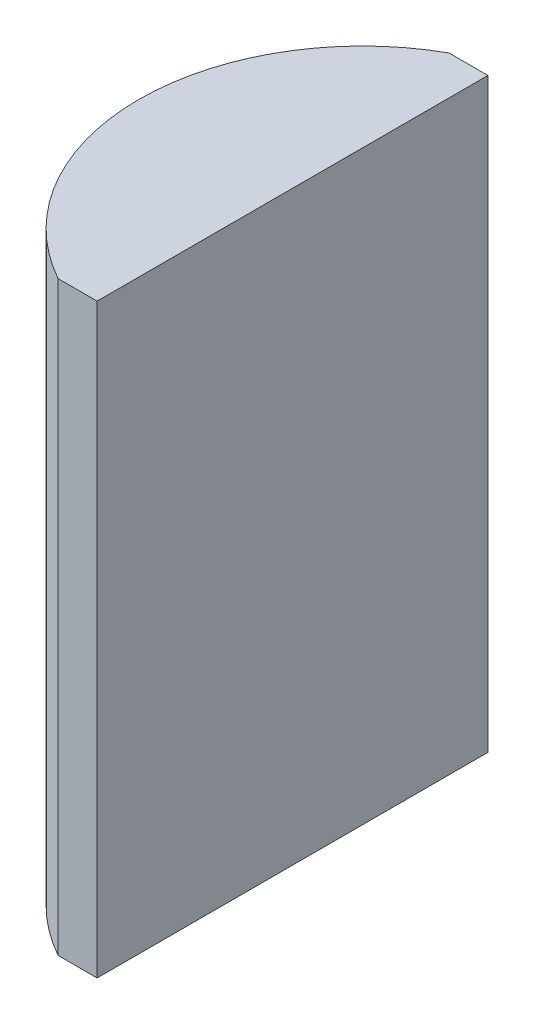
SolidWorks part; units mm, degrees
ref_plane "前视基准面" through (0, 0, 0) normal (0, 0, 1) x (1, 0, 0)
ref_plane "上视基准面" through (0, 0, 0) normal (0, 1, 0) x (1, 0, 0)
ref_plane "右视基准面" through (0, 0, 0) normal (1, 0, 0) x (0, 0, -1)
sketch "草图1" plane through (0, 0, 0) normal (0, 1, 0) x (1, 0, 0)
  line L0 (-137.6835, 0) -> (10.8051, 0) construction
  line L1 (-1.2218, 10) -> (0.7752, 10)
  line L2 (-1.2218, -10) -> (0.7752, -10)
  line L3 (0.7752, 10) -> (0.7752, -10)
  arc A0 (-1.2218, 10) -> (-1.2218, -10) centre (4.3552, 0) ccw
  point P2 (-7.0948, 0)
  point P4 (0.7752, 0)
  dimension "D2" = 10
  dimension "D3" = 11.45
  dimension "D4" = 7.87
  dimension "D1" = 10
extrude "凸台-拉伸1" add sketch "草图1" along normal blind 30
